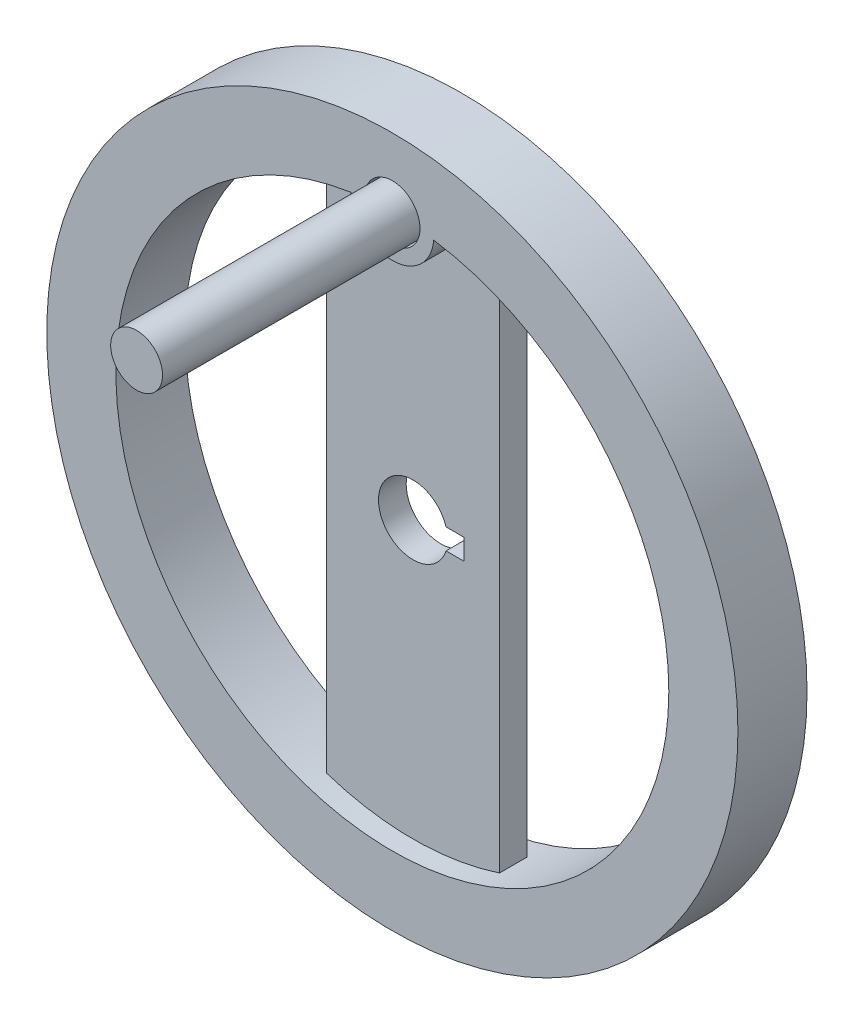
SolidWorks part; units mm, degrees
ref_plane "Front" through (0, 0, 0) normal (0, 0, 1) x (1, 0, 0)
ref_plane "Top" through (0, 0, 0) normal (0, 1, 0) x (1, 0, 0)
ref_plane "Right" through (0, 0, 0) normal (1, 0, 0) x (0, 0, -1)
sketch "草图1" plane through (0, 0, 0) normal (0, 0, 1) x (1, 0, 0)
  line L1 (4.7697, 1.5) -> (7.3697, 1.5)
  line L2 (7.3697, 1.5) -> (7.3697, -1.5)
  line L3 (7.3697, -1.5) -> (4.7697, -1.5)
  circle A0 centre (0, 0) radius 50
  arc A1 (4.7697, 1.5) -> (4.7697, -1.5) centre (0, 0) ccw
  point P3 (7.3697, 0)
  dimension "D1" = 100
  dimension "D2" = 10
  dimension "D3" = 3
  dimension "D4" = 2.6
extrude "凸台-拉伸1" add sketch "草图1" along normal mid plane 10
sketch "草图2" plane through (0, 0, 5) normal (0, 0, 1) x (1, 0, 0)
  circle A0 centre (0, 0) radius 40
  circle A1 centre (0, 0) radius 50
  circle A2 centre (0, 0) radius 50 construction
  dimension "D1" = 0
  dimension "D2" = 10
extrude "切除-拉伸1" cut sketch "草图2" against normal blind 3
mirror "镜向1" about plane through (0, 0, 0) normal (0, 0, 1) of "切除-拉伸1"
sketch "草图3" plane through (0, 0, 2) normal (0, 0, 1) x (1, 0, 0)
  line L0 (-12.5, 37.9967) -> (-12.5, -37.9967)
  line L1 (12.5, 37.9967) -> (12.5, -37.9967)
  arc A0 (12.5, -37.9967) -> (12.5, 37.9967) centre (0, 0) ccw
  circle A2 centre (0, 0) radius 40
  arc A3 (-12.5, 37.9967) -> (-12.5, -37.9967) centre (0, 0) ccw
  dimension "D1" = 0
  dimension "D2" = 25
extrude "切除-拉伸2" cut sketch "草图3" against normal blind 10
sketch "草图4" plane through (0, 0, 2) normal (0, 0, 1) x (1, 0, 0)
  circle A0 centre (0, 40) radius 4
  arc A1 (12.5, 37.9967) -> (-12.5, 37.9967) centre (0, 0) ccw construction
  circle A2 centre (0, 40) radius 6
  dimension "D1" = 12
  dimension "D2" = 8
extrude "凸台-拉伸2" add sketch "草图4" along normal up to surface (3 mm away) separate body up to face at (40, 0, 5)
sketch "草图5" plane through (0, 0, 5) normal (0, 0, 1) x (1, 0, 0)
  circle A0 centre (0, 40) radius 4 construction
  circle A1 centre (0, 40) radius 4
extrude "切除-拉伸3" cut sketch "草图5" against normal up to surface (3 mm away) up to face at (0, 0, 2)
sketch "草图6" plane through (0, 0, 2) normal (0, 0, 1) x (1, 0, 0)
  circle A0 centre (0, 40) radius 3.75
  dimension "D1" = 7.5
extrude "凸台-拉伸3" add sketch "草图6" along normal blind 40
